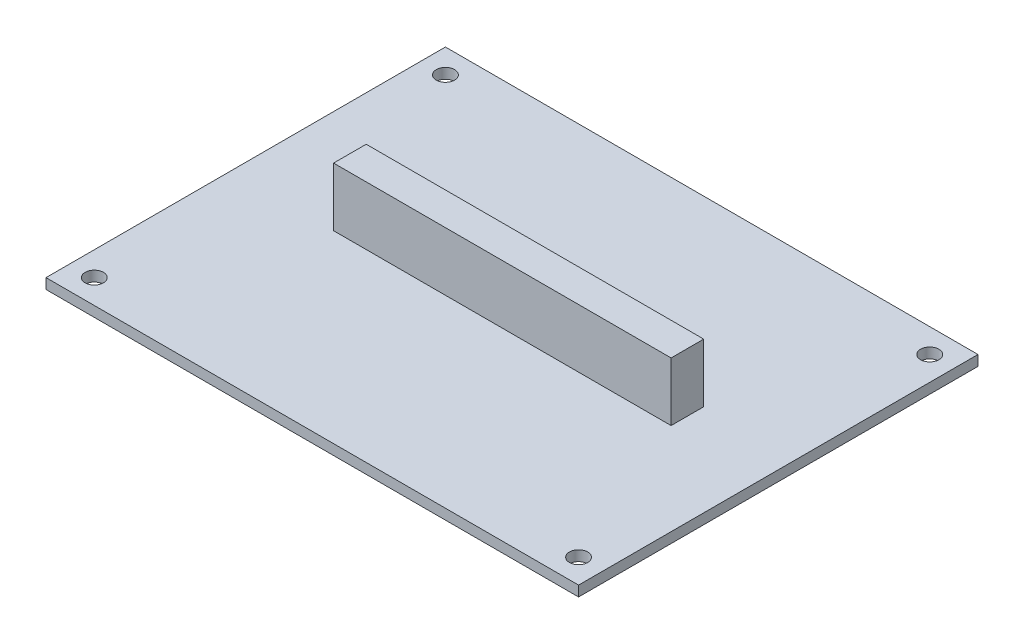
SolidWorks part; units mm, degrees
ref_plane "Front Plane" through (0, 0, 0) normal (0, 0, 1) x (1, 0, 0)
ref_plane "Top Plane" through (0, 0, 0) normal (0, 1, 0) x (1, 0, 0)
ref_plane "Right Plane" through (0, 0, 0) normal (1, 0, 0) x (0, 0, -1)
sketch "Sketch1" plane through (0, 0, 0) normal (0, 1, 0) x (1, 0, 0)
  line L0 (-36.375, 26.375) -> (-36.375, -26.375) construction
  line L1 (-40, -30) -> (40, -30)
  line L2 (-40, -30) -> (-40, 30)
  line L3 (-40, 30) -> (40, 30)
  line L4 (40, -30) -> (40, 30)
  line L5 (-40, -30) -> (40, 30) construction
  line L6 (-40, 30) -> (40, -30) construction
  line L7 (-36.375, 26.375) -> (36.375, 26.375) construction
  circle A4 centre (-36.375, 26.375) radius 1.375
  circle A5 centre (-36.375, -26.375) radius 1.375
  circle A6 centre (36.375, -26.375) radius 1.375
  circle A7 centre (36.375, 26.375) radius 1.375
  point P0 (0, 0)
  point P6 (0, 26.375)
  point P7 (-36.375, 0)
  dimension "D5" = 2.75
  dimension "D1" = 80
  dimension "D2" = 60
  dimension "D3" = 72.75
  dimension "D4" = 52.75
extrude "Boss-Extrude1" add sketch "Sketch1" along normal blind 1.55
sketch "Sketch2" plane through (0, 1.55, 0) normal (0, 1, 0) x (1, 0, 0)
  line L0 (-24.5, 2.6) -> (26.2, 2.6)
  line L1 (26.2, 2.6) -> (26.2, -2.3)
  line L2 (26.2, -2.3) -> (-24.5, -2.3)
  line L3 (-24.5, -2.3) -> (-24.5, 2.6)
  line L4 (40, 30) -> (-40, 30) construction
  line L5 (-40, -30) -> (40, -30) construction
  line L6 (40, -30) -> (40, 30) construction
  line L7 (-40, 30) -> (-40, -30) construction
  dimension "D1" = 32.3
  dimension "D2" = 32.6
  dimension "D3" = 64.5
  dimension "D4" = 66.2
extrude "Boss-Extrude2" add sketch "Sketch2" along normal blind 8.8
